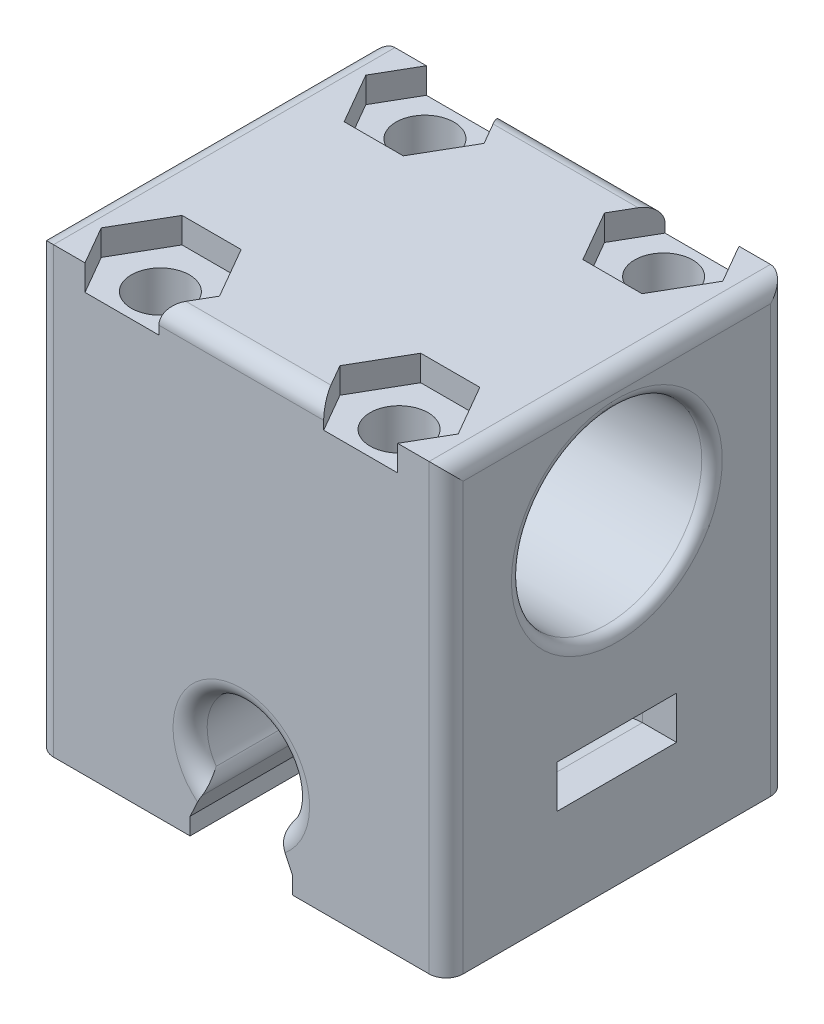
SolidWorks part; units mm, degrees
ref_plane "Alzado" through (0, 0, 0) normal (0, 0, 1) x (1, 0, 0)
ref_plane "Planta" through (0, 0, 0) normal (0, 1, 0) x (1, 0, 0)
ref_plane "Vista lateral" through (0, 0, 0) normal (1, 0, 0) x (0, 0, -1)
sketch "Croquis1" plane through (0, 0, 0) normal (0, -1, 0) x (1, 0, 0)
  line L1 (26.4565, 24.3192) -> (50.4565, 24.3192)
  line L2 (26.4565, 24.3192) -> (26.4565, 4.3192)
  line L3 (26.4565, 4.3192) -> (50.4565, 4.3192)
  line L4 (50.4565, 24.3192) -> (50.4565, 4.3192)
  dimension "D1" = 24
  dimension "D2" = 20
extrude "Saliente-Extruir1" add sketch "Croquis1" against normal blind 25 separate body
sketch "Croquis2" plane through (0, 0, 24.3192) normal (0, 0, 1) x (1, 0, 0)
  line L0 (35.4565, 0) -> (36.3351, 1.8787)
  line L2 (40.5778, 1.8787) -> (41.4565, 0)
  line L3 (41.4565, 0) -> (35.4565, 0)
  line L5 (50.4565, 25) -> (50.4565, 0) construction
  line L6 (50.4565, 0) -> (26.4565, 0) construction
  arc A0 (40.5778, 1.8787) -> (36.3351, 1.8787) centre (38.4565, 4) ccw
  dimension "D1" = 3
  dimension "D4" = 1.0228
  dimension "D5" = 9
  dimension "D2" = 6
  dimension "D3" = 2.074
  dimension "D6" = 25
extrude "Cortar-Extruir1" cut sketch "Croquis2" against normal through all
sketch "Croquis3" plane through (50.4565, 0, 0) normal (1, 0, 0) x (0, 0, -1)
  line L0 (-4.3192, 0) -> (-24.3192, 0) construction
  line L1 (-4.3192, 25) -> (-4.3192, 0) construction
  circle A0 centre (-14.3192, 17.5) radius 5.575
  dimension "D1" = 11.15
  dimension "D2" = 10
  dimension "D3" = 17.5
sketch "Croquis4" plane through (0, 0, 0) normal (0, -1, 0) x (1, 0, 0)
  line L0 (38.4565, 34.8249) -> (38.4565, -1.1794) construction
  line L2 (95.5089, 14.3192) -> (58.9949, 14.3192) construction
  line L4 (26.4565, 24.3192) -> (26.4565, 4.3192) construction
  line L6 (35.4565, 4.3192) -> (35.4565, 24.3192) construction
  circle A0 centre (31.4643, 22.0692) radius 1.7
  circle A1 centre (45.4486, 22.0692) radius 1.7
  circle A2 centre (45.4486, 6.5692) radius 1.7
  circle A3 centre (31.4643, 6.5692) radius 1.7
  dimension "D1" = 12
  dimension "D3" = 3.4
  dimension "D2" = 10
  dimension "D4" = 9.9921
  dimension "D5" = 2.25
extrude "Cortar-Extruir3" cut sketch "Croquis4" against normal through all
sketch "Croquis6" plane through (0, 25, 0) normal (0, 1, 0) x (1, 0, 0)
  line L0 (38.4565, 2.8712) -> (38.4565, -28.7183) construction
  line L1 (42.1324, -4.3131) -> (50.4565, -4.3192)
  line L2 (92.8267, -14.3192) -> (57.3757, -14.3192) construction
  line L5 (50.4565, -4.3192) -> (50.4565, -9.4129)
  line L6 (28.6357, -9.4129) -> (26.4565, -9.4129)
  line L7 (26.4565, -4.3192) -> (26.4565, -9.4129)
  line L8 (48.2772, -9.4129) -> (50.4565, -9.4129)
  line L9 (34.7806, -4.3131) -> (26.4565, -4.3192)
  line L10 (48.2772, -19.2255) -> (50.4565, -19.2255)
  line L12 (50.4565, -24.3192) -> (50.4565, -19.2255)
  line L13 (42.1324, -24.3253) -> (50.4565, -24.3192)
  line L14 (34.7806, -24.3253) -> (26.4565, -24.3192)
  line L15 (26.4565, -24.3192) -> (26.4565, -19.2255)
  line L16 (28.6357, -19.2255) -> (26.4565, -19.2255)
  arc A0 (28.6357, -9.4129) -> (34.7806, -4.3131) centre (31.4643, -6.5692) ccw
  arc A1 (48.2772, -19.2255) -> (42.1324, -24.3253) centre (45.4486, -22.0692) ccw
  arc A2 (28.6357, -19.2255) -> (34.7806, -24.3253) centre (31.4643, -22.0692) cw
  arc A4 (48.2772, -9.4129) -> (42.1324, -4.3131) centre (45.4486, -6.5692) cw
  circle A8 centre (31.4643, -22.0692) radius 1.7 construction
  dimension "D1" = 12
  dimension "D3" = 4.0109
  dimension "D5" = 18.9921
  dimension "D2" = 10
  dimension "D4" = 3.3162
  dimension "D6" = 17.75
  dimension "D7" = 16.8128
extrude "Cortar-Extruir4" [suppressed] cut sketch "Croquis6" against normal blind 2
sketch "Croquis7" [suppressed] plane through (0, 23, 0) normal (0, 1, 0) x (1, 0, 0)
  line L0 (26.4565, -4.3192) -> (28.1572, -4.3192)
  line L1 (26.4565, -4.3192) -> (26.4565, -6.4053)
  line L2 (50.4565, -6.4053) -> (49.4452, -6.4053)
  line L3 (26.4565, -6.4053) -> (27.4677, -6.4053)
  line L4 (50.4565, -4.3192) -> (50.4565, -6.4053)
  line L5 (38.4565, 2.8236) -> (38.4565, -30.8763) construction
  line L6 (93.1844, -14.3192) -> (59.0283, -14.3192) construction
  line L7 (50.4565, -4.3192) -> (48.7558, -4.3192)
  line L8 (50.4565, -24.3192) -> (48.7558, -24.3192)
  line L9 (50.4565, -24.3192) -> (50.4565, -22.2331)
  line L10 (50.4565, -22.2331) -> (49.4452, -22.2331)
  line L11 (26.4565, -22.2331) -> (27.4677, -22.2331)
  line L12 (26.4565, -24.3192) -> (26.4565, -22.2331)
  line L13 (26.4565, -24.3192) -> (28.1572, -24.3192)
  line L16 (26.4565, -4.3192) -> (26.4565, -9.4129) construction
  arc A0 (28.1572, -4.3192) -> (27.4677, -6.4053) centre (31.4643, -6.5692) ccw
  arc A1 (48.7558, -4.3192) -> (49.4452, -6.4053) centre (45.4486, -6.5692) cw
  arc A2 (48.7558, -24.3192) -> (49.4452, -22.2331) centre (45.4486, -22.0692) ccw
  arc A3 (28.1572, -24.3192) -> (27.4677, -22.2331) centre (31.4643, -22.0692) cw
  dimension "D1" = 10
  dimension "D3" = 4
  dimension "D2" = 12
  dimension "D4" = 1.0112
  dimension "D5" = 1.7007
  dimension "D6" = 5.0079
extrude "Cortar-Extruir5" [suppressed] cut sketch "Croquis7" against normal blind 13
sketch "Croquis8" plane through (50.4565, 0, 0) normal (1, 0, 0) x (0, 0, -1)
  line L1 (-17.8192, 7) -> (-10.8192, 7)
  line L2 (-17.8192, 7) -> (-17.8192, 4.5)
  line L3 (-17.8192, 4.5) -> (-10.8192, 4.5)
  line L4 (-10.8192, 7) -> (-10.8192, 4.5)
  line L5 (-4.3192, 0) -> (-24.3192, 0) construction
  dimension "D1" = 7
  dimension "D2" = 2.5
  dimension "D3" = 6.5
  dimension "D4" = 4.5
ref_plane "Plano1" through (0, 0, 10.8192) normal (0, 0, -1) x (-1, 0, 0)
sketch "Croquis9" plane through (0, 0, 10.8192) normal (0, 0, -1) x (-1, 0, 0)
  line L0 (-41.4565, 0) -> (-50.4565, 0) construction
  line L1 (-48.4565, 7) -> (-50.4565, 7)
  line L2 (-43.4565, 2) -> (-43.4565, 0)
  line L3 (-50.4565, 25) -> (-50.4565, 0) construction
  arc A0 (-43.4565, 2) -> (-48.4565, 7) centre (-48.4565, 2) ccw
  dimension "D1" = 5
  dimension "D2" = 2
  dimension "D3" = 2
sweep "Cortar-Barrer2" cut profiles "Croquis8" path "Croquis9"
sketch "Croquis10" plane through (0, 0, 0) normal (0, -1, 0) x (1, 0, 0)
  line L1 (45.9565, 17.8192) -> (46.4565, 17.8192)
  line L2 (45.9565, 17.8192) -> (45.9565, 10.8192)
  line L3 (45.9565, 10.8192) -> (46.4565, 10.8192)
  line L4 (46.4565, 17.8192) -> (46.4565, 10.8192)
  dimension "D1" = 0.5
  dimension "D2" = 7
extrude "Cortar-Extruir6" [suppressed] cut sketch "Croquis10" against normal up to surface (4.5 mm away)
ref_plane "Plano2" through (38.4565, 0, 0) normal (1, 0, 0) x (0, 0, -1)
mirror "Simetría1" about plane through (38.4565, 0, 0) normal (1, 0, 0) of "Cortar-Extruir6", "Cortar-Barrer2"
sketch "Croquis11" plane through (0, 25, 0) normal (0, 1, 0) x (1, 0, 0)
  line L0 (50.4565, -24.3192) -> (26.4565, -24.3192) construction
  line L1 (47.1806, -19.0692) -> (43.7165, -19.0692)
  line L2 (43.7165, -19.0692) -> (41.9845, -22.0692)
  line L3 (41.9845, -22.0692) -> (43.7165, -25.0692)
  line L4 (43.7165, -25.0692) -> (47.1806, -25.0692)
  line L5 (47.1806, -25.0692) -> (48.9127, -22.0692)
  line L6 (48.9127, -22.0692) -> (47.1806, -19.0692)
  line L7 (26.4565, -4.3192) -> (50.4565, -4.3192) construction
  line L8 (34.9284, -22.0692) -> (33.1964, -19.0692)
  line L9 (33.1964, -19.0692) -> (29.7323, -19.0692)
  line L10 (29.7323, -19.0692) -> (28.0002, -22.0692)
  line L11 (28.0002, -22.0692) -> (29.7323, -25.0692)
  line L12 (29.7323, -25.0692) -> (33.1964, -25.0692)
  line L13 (33.1964, -25.0692) -> (34.9284, -22.0692)
  line L14 (34.9284, -6.5692) -> (33.1964, -3.5692)
  line L15 (33.1964, -3.5692) -> (29.7323, -3.5692)
  line L16 (29.7323, -3.5692) -> (28.0002, -6.5692)
  line L17 (28.0002, -6.5692) -> (29.7323, -9.5692)
  line L18 (29.7323, -9.5692) -> (33.1964, -9.5692)
  line L19 (33.1964, -9.5692) -> (34.9284, -6.5692)
  line L20 (47.1806, -9.5692) -> (48.9127, -6.5692)
  line L21 (48.9127, -6.5692) -> (47.1806, -3.5692)
  line L22 (47.1806, -3.5692) -> (43.7165, -3.5692)
  line L23 (43.7165, -3.5692) -> (41.9845, -6.5692)
  line L24 (41.9845, -6.5692) -> (43.7165, -9.5692)
  line L25 (43.7165, -9.5692) -> (47.1806, -9.5692)
  circle A0 centre (45.4486, -22.0692) radius 3 construction
  circle A1 centre (31.4643, -22.0692) radius 3 construction
  circle A2 centre (31.4643, -6.5692) radius 3 construction
  circle A3 centre (45.4486, -6.5692) radius 3 construction
extrude "Cortar-Extruir7" cut sketch "Croquis11" against normal blind 1.5
extrude "Cortar-Extruir8" cut sketch "Croquis3" against normal blind 40
sketch "Croquis13" plane through (0, 0, 0) normal (0, -1, 0) x (1, 0, 0)
  line L1 (50.4565, 24.3192) -> (41.4565, 24.3192)
  line L2 (50.4565, 24.3192) -> (50.4565, 4.3192)
  line L3 (50.4565, 4.3192) -> (41.4565, 4.3192)
  line L4 (41.4565, 24.3192) -> (41.4565, 4.3192)
  line L5 (45.9565, 17.8192) -> (43.4565, 17.8192)
  line L6 (45.9565, 17.8192) -> (45.9565, 10.8192)
  line L7 (45.9565, 10.8192) -> (43.4565, 10.8192)
  line L8 (43.4565, 17.8192) -> (43.4565, 10.8192)
  circle A0 centre (45.4486, 22.0692) radius 1.7
  circle A1 centre (45.4486, 6.5692) radius 1.7
extrude "Saliente-Extruir2" add sketch "Croquis13" along normal blind 1
sketch "Croquis14" plane through (0, 0, 0) normal (0, -1, 0) x (1, 0, 0)
  line L1 (35.4565, 24.3192) -> (26.4565, 24.3192)
  line L2 (35.4565, 24.3192) -> (35.4565, 4.3192)
  line L3 (35.4565, 4.3192) -> (26.4565, 4.3192)
  line L4 (26.4565, 24.3192) -> (26.4565, 4.3192)
  line L5 (33.4565, 17.8192) -> (30.9565, 17.8192)
  line L6 (33.4565, 17.8192) -> (33.4565, 10.8192)
  line L7 (33.4565, 10.8192) -> (30.9565, 10.8192)
  line L8 (30.9565, 17.8192) -> (30.9565, 10.8192)
  circle A0 centre (31.4643, 22.0692) radius 1.7
  circle A1 centre (31.4643, 6.5692) radius 1.7
extrude "Saliente-Extruir3" add sketch "Croquis14" along normal blind 1
fillet "Redondeo1" radius 1 12 edges at (38.4565, 25, 24.3192) (38.4565, 25, 4.3192) (26.4565, 25, 14.3192) (26.4565, 12, 4.3192) (26.4565, 12, 24.3192) (50.4565, 12, 4.3192) (50.4565, 25, 14.3192) (50.4565, 12, 24.3192) (40.5778, 1.8787, 14.3192) (36.3351, 1.8787, 14.3192) (38.4565, 7, 4.3192) (38.4565, 7, 24.3192)
fillet "Redondeo3" radius 0.6 2 edges at (50.4565, 17.5, 8.7442) (26.4565, 17.5, 19.8942)
